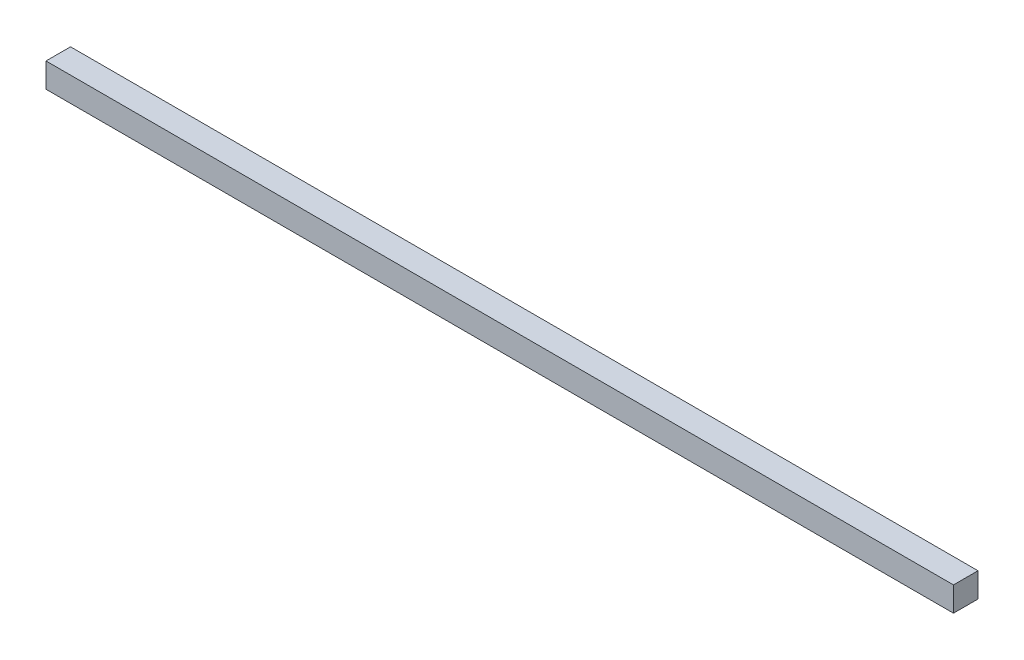
SolidWorks part; units mm, degrees
ref_plane "Front Plane" through (0, 0, 0) normal (0, 0, 1) x (1, 0, 0)
ref_plane "Top Plane" through (0, 0, 0) normal (0, 1, 0) x (1, 0, 0)
ref_plane "Right Plane" through (0, 0, 0) normal (1, 0, 0) x (0, 0, -1)
sketch "Sketch1" plane through (0, 0, 0) normal (1, 0, 0) x (0, 0, -1)
  line L1 (0, 0) -> (25.4, 0)
  line L2 (0, 0) -> (0, 25.4)
  line L3 (0, 25.4) -> (25.4, 25.4)
  line L4 (25.4, 0) -> (25.4, 25.4)
  dimension "D1" = 25.4
  dimension "D2" = 25.4
extrude "Boss-Extrude2" add sketch "Sketch1" along normal blind 939.8
